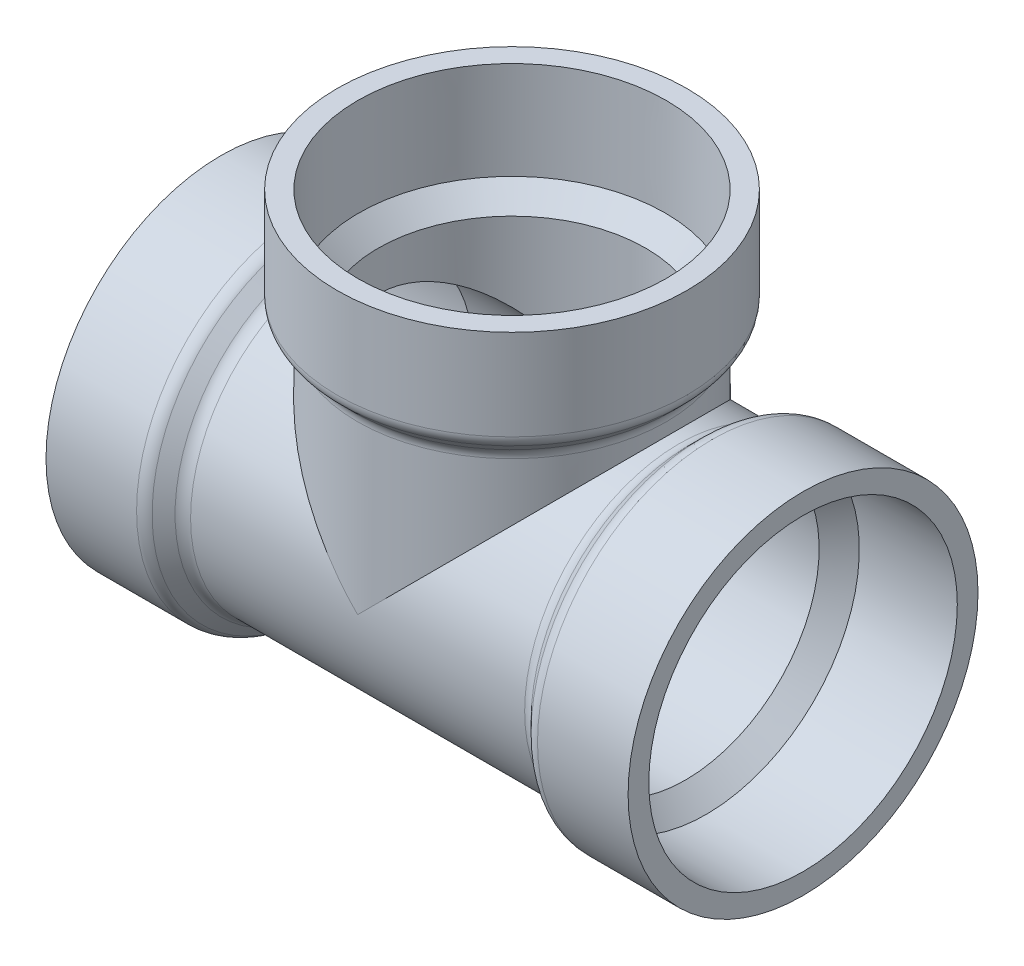
SolidWorks part; units mm, degrees
ref_plane "Front Plane" through (0, 0, 0) normal (0, 0, 1) x (1, 0, 0)
ref_plane "Top Plane" through (0, 0, 0) normal (0, 1, 0) x (1, 0, 0)
ref_plane "Right Plane" through (0, 0, 0) normal (1, 0, 0) x (0, 0, -1)
sketch "Sketch0" plane through (0, 0, 0) normal (0, 0, 1) x (1, 0, 0)
  line L0 (-57.15, 0) -> (0, 0) construction
  line L1 (0, 0) -> (0, 57.15) construction
  line L2 (-38.1, 0) -> (0, 0) construction
  line L3 (0, 0) -> (0, 38.1) construction
  line L4 (-57.15, 34.3535) -> (-57.15, -34.3535) construction
  line L5 (-38.1, 30.099) -> (-57.15, 30.2895) construction
  line L6 (-38.1, 30.099) -> (-38.1, -30.099) construction
  line L7 (-38.1, -30.099) -> (-57.15, -30.2895) construction
  line L8 (-57.15, 30.2895) -> (-57.15, -30.2895) construction
  line L9 (-34.3535, 57.15) -> (34.3535, 57.15) construction
  line L10 (-30.2895, 57.15) -> (30.2895, 57.15) construction
  line L11 (30.2895, 57.15) -> (30.099, 38.1) construction
  line L12 (30.099, 38.1) -> (-30.099, 38.1) construction
  line L13 (-30.099, 38.1) -> (-30.2895, 57.15) construction
  line L14 (-38.1, 26.2509) -> (-38.1, -26.2509) construction
  line L15 (-38.1, -26.2509) -> (-38.1, -30.3149) construction
  line L16 (-57.15, -30.2895) -> (-57.15, -34.3535) construction
  line L17 (26.2509, 38.1) -> (30.3149, 38.1) construction
  line L18 (-26.2509, 38.1) -> (26.2509, 38.1) construction
  line L19 (30.2895, 57.15) -> (34.3535, 57.15) construction
sketch "Sketch1" plane through (0, 0, 0) normal (0, 0, 1) x (1, 0, 0)
  line L0 (-57.15, 0) -> (0, 0) construction
  line L1 (-57.15, 0) -> (0, 0) construction
  line L2 (-38.1, -34.3535) -> (-34.0614, -30.3149)
  line L3 (-57.15, -34.3535) -> (-38.1, -34.3535)
  line L4 (-57.15, -34.3535) -> (-57.15, -30.2895)
  line L5 (-57.15, -30.2895) -> (-38.1, -30.099)
  line L6 (-38.1, -34.3535) -> (-38.1, -30.099) construction
  line L7 (-34.0614, -30.3149) -> (-34.0614, -26.2509)
  line L8 (-34.0614, -26.2509) -> (-38.1, -30.099)
  line L9 (-38.1, -34.3535) -> (-34.0614, -34.3535) construction
  line L10 (-38.1, -26.2509) -> (-34.0614, -26.2509) construction
  line L11 (-34.0614, -34.3535) -> (-34.0614, -30.3149) construction
  line L12 (-38.1, -30.3149) -> (-34.0614, -30.3149) construction
revolve "Revolve1" add sketch "Sketch1" angle 360 about L1
mirror "Mirror1" about plane through (0, 0, 0) normal (1, 0, 0) of bodies 102
sketch "Sketch2" plane through (0, 0, 0) normal (0, 0, 1) x (1, 0, 0)
  line L0 (30.2895, 57.15) -> (30.099, 38.1)
  line L1 (30.099, 38.1) -> (34.3535, 38.1) construction
  line L2 (34.3535, 38.1) -> (34.3535, 57.15)
  line L3 (34.3535, 57.15) -> (30.2895, 57.15)
  line L4 (0, 0) -> (0, 57.15) construction
  line L5 (0, 0) -> (0, 57.15) construction
  line L6 (30.099, 38.1) -> (26.2509, 34.0614)
  line L7 (26.2509, 38.1) -> (26.2509, 34.0614) construction
  line L8 (34.3535, 38.1) -> (30.3149, 34.0614)
  line L9 (30.3149, 34.0614) -> (26.2509, 34.0614)
  line L10 (34.3535, 38.1) -> (34.3535, 34.0614) construction
  line L11 (34.3535, 34.0614) -> (30.3149, 34.0614) construction
  line L12 (30.3149, 38.1) -> (30.3149, 34.0614) construction
revolve "Revolve2" add sketch "Sketch2" angle 360 about L5
sketch "Sketch3" plane through (-34.0614, 0, 0) normal (1, 0, 0) x (0, 0, -1)
  circle A0 centre (0, 0) radius 26.2509
  circle A1 centre (0, 0) radius 30.3149
sketch "Sketch4" plane through (0, 0, 0) normal (0, 0, 1) x (1, 0, 0)
  line L0 (-57.15, 0) -> (0, 0) construction
  line L1 (0, 0) -> (0, 57.15) construction
  line L2 (-57.15, 0) -> (-34.0614, 0) construction
  line L3 (0, 34.0614) -> (0, 57.15) construction
  line L4 (-34.0614, -30.3149) -> (-34.0614, 30.3149) construction
  arc A0 (-34.0614, 0) -> (0, 34.0614) centre (-34.0614, 34.0614) ccw
sketch "Sketch5" plane through (-34.0614, 0, 0) normal (1, 0, 0) x (0, 0, -1)
  circle A0 centre (0, 0) radius 30.3149 construction
  circle A1 centre (0, 0) radius 30.3149
extrude "Boss-Extrude1" add sketch "Sketch5" along normal up to surface (68.1228 mm away) up to face at (34.0614, 0, 26.2509)
sketch "Sketch6" plane through (0, 34.0614, 0) normal (0, -1, 0) x (1, 0, 0)
  circle A0 centre (0, 0) radius 30.3149 construction
  circle A1 centre (0, 0) radius 30.3149
extrude "Boss-Extrude2" add sketch "Sketch6" along normal up to surface (34.0614 mm away) up to plane "Top Plane"
fillet "Fillet1" radius 3.048 6 edges at (0, 38.1, -34.3535) (-38.1, 0, 34.3535) (0, 34.0614, -30.3149) (-34.0614, 0, -30.3149) (38.1, 0, 34.3535) (34.0614, 0, 30.3149)
sketch "Sketch7" plane through (0, 0, 0) normal (0, 0, 1) x (1, 0, 0)
  line L0 (-57.15, 0) -> (57.15, 0)
  line L1 (-57.15, 34.3535) -> (-57.15, -34.3535) construction
  line L2 (57.15, -34.3535) -> (57.15, 34.3535) construction
  line L3 (0, 0) -> (0, 26.2509) construction
  line L4 (0, 0) -> (0, 57.15) construction
  line L5 (-57.15, 0) -> (-57.15, 30.2895)
  line L6 (-57.15, 30.2895) -> (-38.1, 30.099)
  line L7 (-38.1, 30.099) -> (-34.0614, 26.2509)
  line L8 (38.1, 30.099) -> (34.0614, 26.2509)
  line L9 (57.15, 30.2895) -> (38.1, 30.099)
  line L10 (57.15, 0) -> (57.15, 30.2895)
  line L11 (-34.0614, 26.2509) -> (34.0614, 26.2509)
revolve "Cut-Revolve1" cut sketch "Sketch7" angle 360 about L0
sketch "Sketch8" plane through (0, 0, 0) normal (0, 0, 1) x (1, 0, 0)
  line L0 (30.2895, 57.15) -> (30.099, 38.1)
  line L1 (30.099, 38.1) -> (26.2509, 34.0614)
  line L2 (26.2509, 34.0614) -> (26.2509, 0)
  line L3 (26.2509, 0) -> (0, 0)
  line L4 (0, 0) -> (0, 57.15)
  line L5 (-34.3535, 57.15) -> (34.3535, 57.15) construction
  line L6 (0, 57.15) -> (30.2895, 57.15)
revolve "Cut-Revolve4" cut sketch "Sketch8" angle 360 about L4
equation "\"D1@Fillet1\" = \"H@Sketch0\" * 3 / 4"
